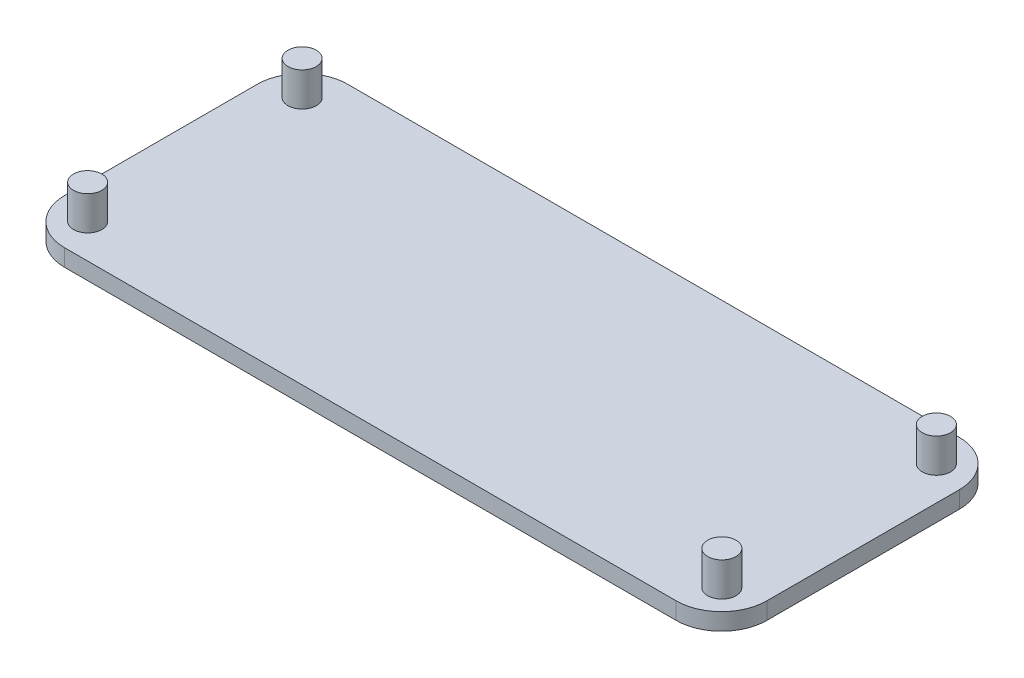
SolidWorks part; units mm, degrees
ref_plane "Alzado" through (0, 0, 0) normal (0, 0, 1) x (1, 0, 0)
ref_plane "Planta" through (0, 0, 0) normal (0, 1, 0) x (1, 0, 0)
ref_plane "Vista lateral" through (0, 0, 0) normal (1, 0, 0) x (0, 0, -1)
sketch "Croquis1" plane through (0, 0, 0) normal (0, 1, 0) x (1, 0, 0)
  line L1 (-31, 12.5) -> (31, 12.5)
  line L2 (-31, 12.5) -> (-31, -12.5)
  line L3 (-31, -12.5) -> (31, -12.5)
  line L4 (31, 12.5) -> (31, -12.5)
  line L5 (-31, 12.5) -> (31, -12.5) construction
  line L6 (-31, -12.5) -> (31, 12.5) construction
  point P0 (0, 0)
  dimension "D1" = 62
  dimension "D2" = 25
extrude "Saliente-Extruir1" add sketch "Croquis1" along normal blind 1.5
fillet "Redondeo1" radius 4 4 edges at (-31, 0.75, 12.5) (31, 0.75, 12.5) (31, 0.75, -12.5) (-31, 0.75, -12.5)
sketch "Croquis2" plane through (0, 1.5, 0) normal (0, 1, 0) x (1, 0, 0)
  line L1 (-28, 9.47) -> (28, 9.47) construction
  line L2 (-28, 9.47) -> (-28, -9.47) construction
  line L3 (-28, -9.47) -> (28, -9.47) construction
  line L4 (28, 9.47) -> (28, -9.47) construction
  line L5 (-28, 9.47) -> (28, -9.47) construction
  line L6 (-28, -9.47) -> (28, 9.47) construction
  circle A0 centre (-28, 9.47) radius 1.25
  circle A1 centre (28, 9.47) radius 1.25
  circle A2 centre (28, -9.47) radius 1.25
  circle A3 centre (-28, -9.47) radius 1.25
  point P0 (0, 0)
  dimension "D3" = 2.5
  dimension "D1" = 56
  dimension "D2" = 18.94
extrude "Saliente-Extruir2" add sketch "Croquis2" along normal blind 3
